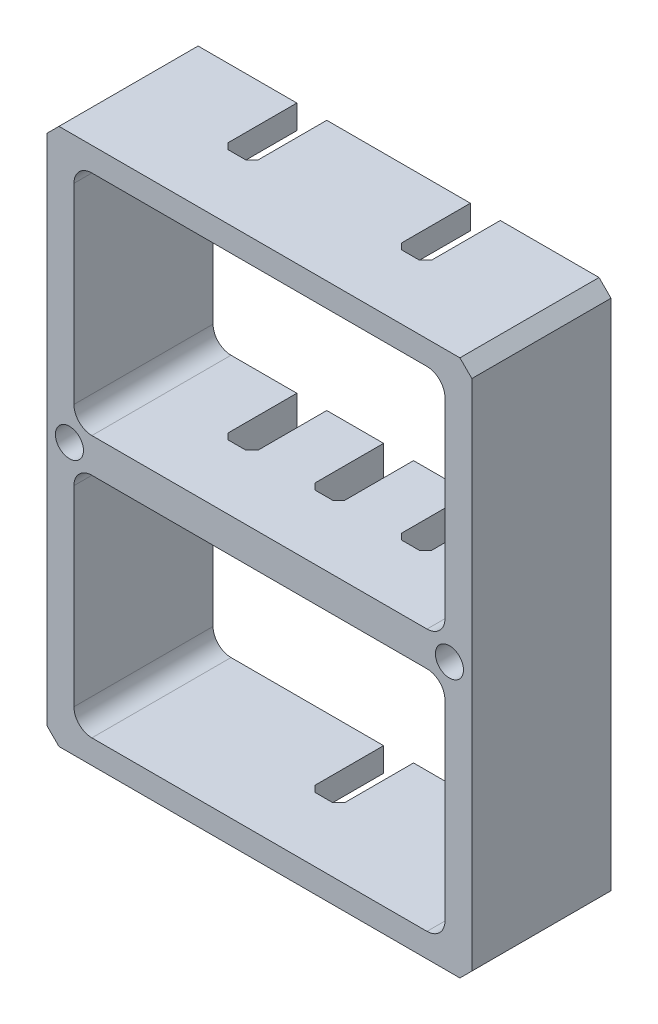
SolidWorks part; units mm, degrees
ref_plane "Front Plane" through (0, 0, 0) normal (0, 0, 1) x (1, 0, 0)
ref_plane "Top Plane" through (0, 0, 0) normal (0, 1, 0) x (1, 0, 0)
ref_plane "Right Plane" through (0, 0, 0) normal (1, 0, 0) x (0, 0, -1)
sketch "Sketch1" plane through (0, 0, 0) normal (0, 0, 1) x (1, 0, 0)
  line L4 (30.226, -70.2945) -> (30.226, -77.9145) construction
  line L5 (15.494, -69.7865) -> (30.226, -69.7865) construction
  line L6 (15.494, -69.7865) -> (15.494, -78.4225) construction
  line L7 (15.494, -78.4225) -> (30.226, -78.4225) construction
  line L8 (10.033, -79.9465) -> (31.877, -79.9465)
  line L9 (31.877, -79.9465) -> (31.877, -64.0516)
  line L10 (35.687, -57.15) -> (13.843, -57.15)
  line L11 (13.843, -57.15) -> (13.843, -73.0449)
  line L12 (13.843, -79.9465) -> (31.877, -79.9465)
  line L13 (31.877, -79.9465) -> (31.877, -57.15)
  line L14 (31.877, -57.15) -> (13.843, -57.15)
  line L15 (13.843, -57.15) -> (13.843, -79.9465)
  line L16 (30.226, -69.7865) -> (30.226, -78.4225) construction
  line L17 (22.86, -78.4225) -> (22.86, -69.7865) construction
  line L18 (15.494, -74.1045) -> (30.226, -74.1045) construction
  line L19 (16.002, -69.7865) -> (29.718, -69.7865) construction
  line L20 (15.494, -77.9145) -> (15.494, -70.2945) construction
  line L21 (29.718, -78.4225) -> (16.002, -78.4225) construction
  line L22 (14.986, -69.2785) -> (30.734, -69.2785)
  line L23 (30.734, -69.2785) -> (30.734, -78.9305)
  line L24 (14.986, -78.9305) -> (30.734, -78.9305)
  line L25 (14.986, -69.2785) -> (14.986, -78.9305)
  line L26 (13.843, -68.5482) -> (31.877, -68.5482) construction
  line L27 (14.986, -67.818) -> (14.986, -58.166)
  line L28 (14.986, -58.166) -> (30.734, -58.166)
  line L29 (30.734, -67.818) -> (30.734, -58.166)
  line L30 (14.986, -67.818) -> (30.734, -67.818)
  line L51 (31.877, -64.0516) -> (35.687, -60.2416)
  line L53 (35.687, -60.2416) -> (35.687, -57.15)
  line L55 (13.843, -73.0449) -> (10.033, -76.8549)
  line L57 (10.033, -76.8549) -> (10.033, -79.9465)
  point P208 (22.86, -74.1045)
  dimension "D2" = 0.508
  dimension "D1" = 0.508
extrude "Boss-Extrude1" add sketch "Sketch1" along normal offset from surface (5.9055 mm away) 1.5875 contours L14 L15 L12 L13 L30 L27 L28 L29 L25 L22 L23 L24
sketch "Sketch2" plane through (0, 0, 0) normal (0, 0, -1) x (-1, 0, 0)
  line L0 (-18.796, -57.404) -> (-19.558, -57.404) construction
  line L3 (-26.162, -57.404) -> (-26.924, -57.404) construction
  line L5 (-23.241, -68.58) -> (-22.479, -68.58) construction
  line L8 (-18.796, -68.5165) -> (-19.558, -68.5165) construction
  line L9 (-26.162, -68.5165) -> (-26.924, -68.5165) construction
  line L10 (-23.241, -79.6925) -> (-22.479, -79.6925) construction
  line L11 (-22.86, -78.9305) -> (-22.86, -79.9465)
  line L12 (-30.734, -78.9305) -> (-14.986, -78.9305) construction
  line L13 (-31.877, -79.9465) -> (-13.843, -79.9465) construction
  line L14 (-19.177, -57.15) -> (-19.177, -58.166)
  line L15 (-13.843, -57.15) -> (-31.877, -57.15) construction
  line L16 (-30.734, -58.166) -> (-14.986, -58.166) construction
  line L17 (-26.543, -57.15) -> (-26.543, -58.166)
  line L18 (-22.86, -69.2785) -> (-22.86, -67.818)
  line L19 (-30.734, -69.2785) -> (-14.986, -69.2785) construction
  line L20 (-30.734, -67.818) -> (-14.986, -67.818) construction
  line L21 (-19.177, -69.2785) -> (-19.177, -67.818)
  line L22 (-26.543, -69.2785) -> (-26.543, -67.818)
  point P0 (-19.177, -57.404)
  point P1 (-26.543, -57.404)
  point P4 (-22.86, -68.58)
  point P7 (-19.177, -68.5165)
  point P10 (-26.543, -68.5165)
  point P13 (-22.86, -79.6925)
extrude "Cut-Extrude-Thin2" cut sketch "Sketch2" against normal blind 3.175 thin contours L14 | L17 | L21 | L18 | L22 | L11 thin type mid plane wall 1.27
chamfer "Chamfer1" distance 0.254 angle 45 12 edges at (23.495, -79.4385, 3.175) (22.225, -79.4385, 3.175) (27.178, -68.5482, 3.175) (25.908, -68.5482, 3.175) (22.225, -68.5482, 3.175) (23.495, -68.5482, 3.175) (19.812, -68.5482, 3.175) (18.542, -68.5482, 3.175) (18.542, -57.658, 3.175) (19.812, -57.658, 3.175) (25.908, -57.658, 3.175) (27.178, -57.658, 3.175)
chamfer "Chamfer2" distance 0.508 angle 45 4 edges at (31.877, -57.15, 2.9528) (13.843, -57.15, 2.9528) (13.843, -79.9465, 2.9528) (31.877, -79.9465, 2.9528)
fillet "Fillet1" radius 0.762 8 edges at (14.986, -78.9305, 2.9528) (30.734, -78.9305, 2.9528) (30.734, -69.2785, 2.9528) (14.986, -69.2785, 2.9528) (14.986, -67.818, 2.9528) (30.734, -67.818, 2.9528) (14.986, -58.166, 2.9528) (30.734, -58.166, 2.9528)
hole_wizard "#0-80 Tapped Hole1" positions "Sketch4" profile "Sketch3" tap size "#0-80" standard "ANSI Inch" end condition through all
sketch "Sketch4" plane through (0, 0, 0) normal (0, 0, -1) x (-1, 0, 0)
  line L0 (-15.748, -69.2785) -> (-15.748, -67.818) construction
  line L2 (-15.748, -68.5482) -> (-13.843, -68.5482) construction
  line L3 (-13.843, -57.658) -> (-13.843, -79.4385) construction
  line L5 (-22.86, -57.15) -> (-22.86, -79.9465) construction
  line L6 (-25.908, -57.15) -> (-19.812, -57.15) construction
  line L7 (-22.479, -79.9465) -> (-23.241, -79.9465) construction
  point P12 (-14.7955, -68.5482)
  point P25 (-30.9245, -68.5482)
sketch "Sketch3" plane through (30.9245, -68.5482, 0) normal (1, 0, 0) x (0, 1, 0)
  line L0 (0, 0) -> (0, 5.9055)
  line L1 (0, 5.9055) -> (0.5956, 5.9055)
  line L2 (0.5956, 5.9055) -> (0.5956, 0)
  line L5 (0.5956, 0) -> (0, 0)
  line L11 (0, -6.35) -> (0, 107.95) construction
  dimension "Thru Tap Drill Dia." = 1.1913
  dimension "Thru Tap Drill Depth" = 5.9055
cosmetic thread "Hole Thread1" parameters "D2"=1.524
cosmetic thread "Hole Thread2" parameters "D2"=1.524
